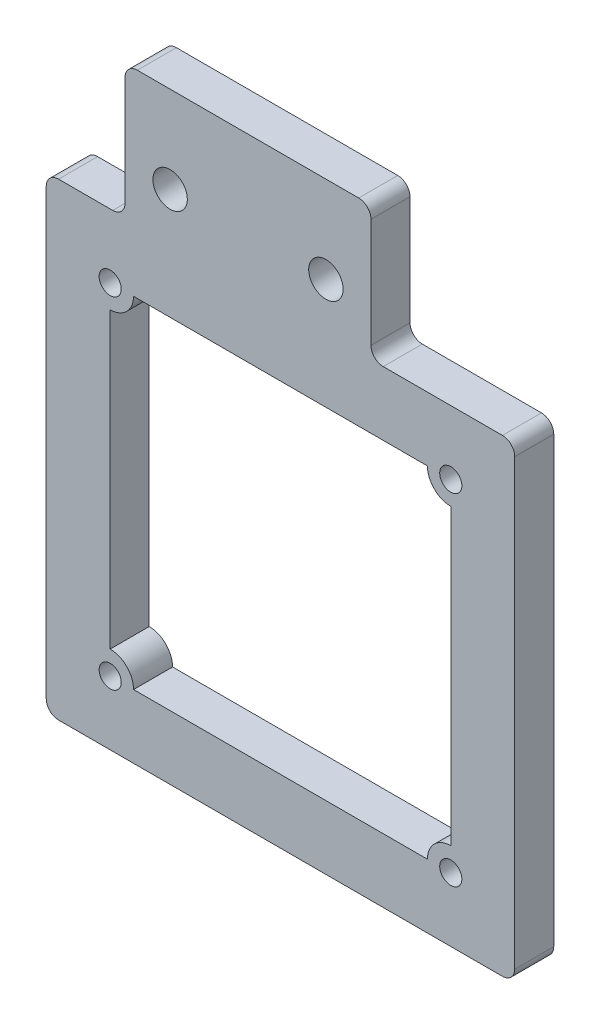
SolidWorks part; units mm, degrees
ref_plane "Front Plane" through (0, 0, 0) normal (0, 0, 1) x (1, 0, 0)
ref_plane "Top Plane" through (0, 0, 0) normal (0, 1, 0) x (1, 0, 0)
ref_plane "Right Plane" through (0, 0, 0) normal (1, 0, 0) x (0, 0, -1)
sketch "Sketch1" plane through (0, 0, 0) normal (0, 0, 1) x (1, 0, 0)
  line L0 (31.6909, -38.1) -> (31.6909, 0) construction
  line L1 (-6.4091, -38.1) -> (31.6909, -38.1) construction
  line L2 (-6.4091, 0) -> (-6.4091, -38.1) construction
  line L3 (31.6909, 0) -> (-6.4091, 0) construction
  line L4 (0, 14.3492) -> (0, 0) construction
  line L5 (16.335, 3.8116) -> (20, 3.8116) construction
  line L6 (20, 14.3492) -> (20, 0) construction
  line L7 (31.6909, -38.1) -> (31.6909, 0)
  line L8 (-6.4091, -38.1) -> (31.6909, -38.1)
  line L9 (-6.4091, 0) -> (-6.4091, -38.1)
  line L10 (31.6909, 0) -> (20, 0)
  line L11 (0, 10.8755) -> (0, 0)
  line L12 (3.665, 3.8116) -> (0, 3.8116) construction
  line L13 (20, 10.8755) -> (20, 0)
  line L14 (0, 0) -> (-6.4091, 0)
  line L15 (20, 10.8755) -> (0, 10.8755)
  line L16 (10, 10.8755) -> (10, -38.1) construction
  line L17 (26.4909, -7.1) -> (26.4909, -31)
  line L18 (24.5909, -32.9) -> (0.6909, -32.9)
  line L19 (-1.2091, -7.1) -> (-1.2091, -31)
  line L22 (24.5909, -5.2) -> (0.6909, -5.2)
  circle A3 centre (-1.2091, -5.2) radius 0.7556 construction
  circle A4 centre (26.4909, -32.9) radius 0.9
  circle A5 centre (-1.2091, -32.9) radius 0.9
  circle A6 centre (-1.2091, -5.2) radius 0.9
  circle A7 centre (26.4909, -5.2) radius 0.9
  circle A8 centre (16.335, 3.8116) radius 1.4
  circle A9 centre (3.665, 3.8116) radius 1.4
  arc A10 (26.4909, -7.1) -> (24.5909, -5.2) centre (26.4909, -5.2) cw
  arc A11 (26.4909, -31) -> (24.5909, -32.9) centre (26.4909, -32.9) ccw
  arc A12 (0.6909, -32.9) -> (-1.2091, -31) centre (-1.2091, -32.9) ccw
  arc A13 (-1.2091, -7.1) -> (0.6909, -5.2) centre (-1.2091, -5.2) ccw
  circle A15 centre (-1.2091, -32.9) radius 0.7556 construction
  circle A16 centre (26.4909, -32.9) radius 0.9271 construction
  dimension "D1" = 2.8
  dimension "D2" = 1
  dimension "D3" = 1.8
extrude "Boss-Extrude1" add sketch "Sketch1" along normal blind 3.175 contours A5 | A4 | A9 | L13 L10 L7 L8 L9 L14 L11 L15 | L19 A12 L18 A11 L17 A10 L22 A13 | A7 | A6 | A8
fillet "Fillet1" radius 1 8 edges at (20, 0, 1.5875) (20, 10.8755, 1.5875) (0, 10.8755, 1.5875) (0, 0, 1.5875) (-6.4091, 0, 1.5875) (-6.4091, -38.1, 1.5875) (31.6909, 0, 1.5875) (31.6909, -38.1, 1.5875)
